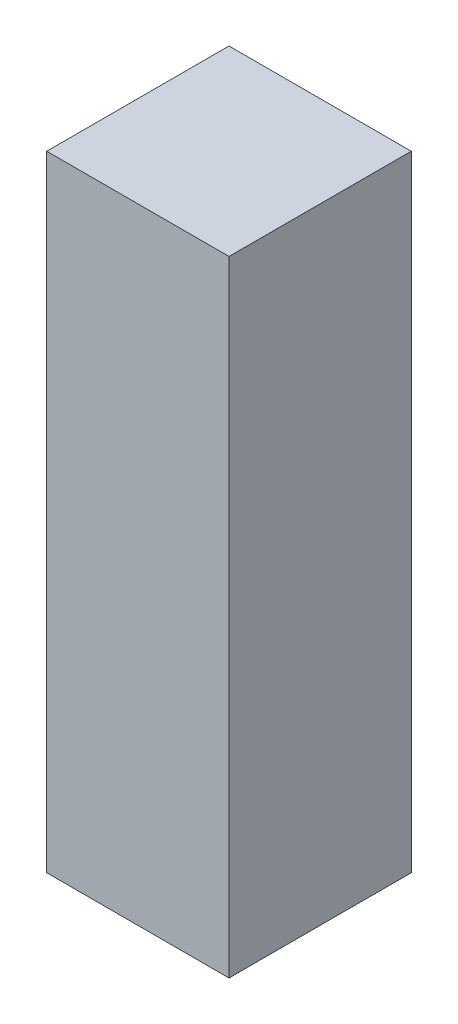
SolidWorks part; units mm, degrees
material "Pine"
ref_plane "Front Plane" through (0, 0, 0) normal (0, 0, 1) x (1, 0, 0)
ref_plane "Top Plane" through (0, 0, 0) normal (0, 1, 0) x (1, 0, 0)
ref_plane "Right Plane" through (0, 0, 0) normal (1, 0, 0) x (0, 0, -1)
sketch "Sketch1" plane through (0, 0, 0) normal (0, 1, 0) x (1, 0, 0)
  line L1 (-44.45, -44.45) -> (44.45, -44.45)
  line L2 (-44.45, -44.45) -> (-44.45, 44.45)
  line L3 (-44.45, 44.45) -> (44.45, 44.45)
  line L4 (44.45, -44.45) -> (44.45, 44.45)
  line L5 (-44.45, -44.45) -> (44.45, 44.45) construction
  line L6 (-44.45, 44.45) -> (44.45, -44.45) construction
  point P0 (0, 0)
  dimension "D1" = 88.9
extrude "Boss-Extrude1" add sketch "Sketch1" along normal blind 304.8
